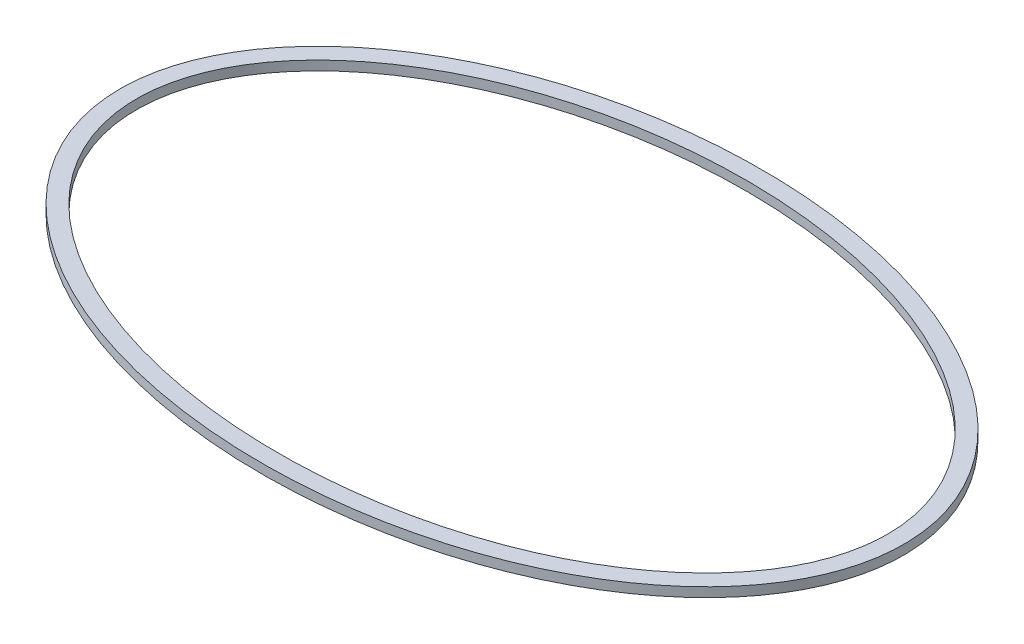
SolidWorks part; units mm, degrees
ref_plane "Front Plane" through (0, 0, 0) normal (0, 0, 1) x (1, 0, 0)
ref_plane "Top Plane" through (0, 0, 0) normal (0, 1, 0) x (1, 0, 0)
ref_plane "Right Plane" through (0, 0, 0) normal (1, 0, 0) x (0, 0, -1)
sketch "Sketch1" plane through (0, 0, 0) normal (0, 1, 0) x (1, 0, 0)
  ellipse E0 centre (-105.4956, 43.4586) end of major axis (94.5044, 42.9218) minor radius 125.0005
  ellipse E1 centre (-105.4956, 43.4586) end of major axis (103.4846, 42.325) minor radius 134.002
  dimension "D1" = 250
  dimension "D2" = 400
  dimension "D3" = 9
  dimension "D4" = 9
extrude "Boss-Extrude1" add sketch "Sketch1" along normal blind 5
equation "\"waist_length\"= 400"
equation "\"waist_width\"= 250"
equation "\"D1@Sketch1\"=\"waist_width\""
equation "\"D2@Sketch1\"=\"waist_length\""
equation "\"buckle_thickness\"= 8"
equation "\"visable_border\"= 3"
equation "\"cutout_border\"= 1.5"
equation "\"belt_thickness\"= 9"
equation "\"belt_width\"= 5"
equation "\"belt_placement\"= 7.5"
equation "\"base_size\"= 30"
equation "\"D3@Sketch1\"=\"belt_thickness\""
equation "\"D4@Sketch1\"=\"belt_thickness\""
equation "\"D1@Boss-Extrude1\"=\"belt_width\""
